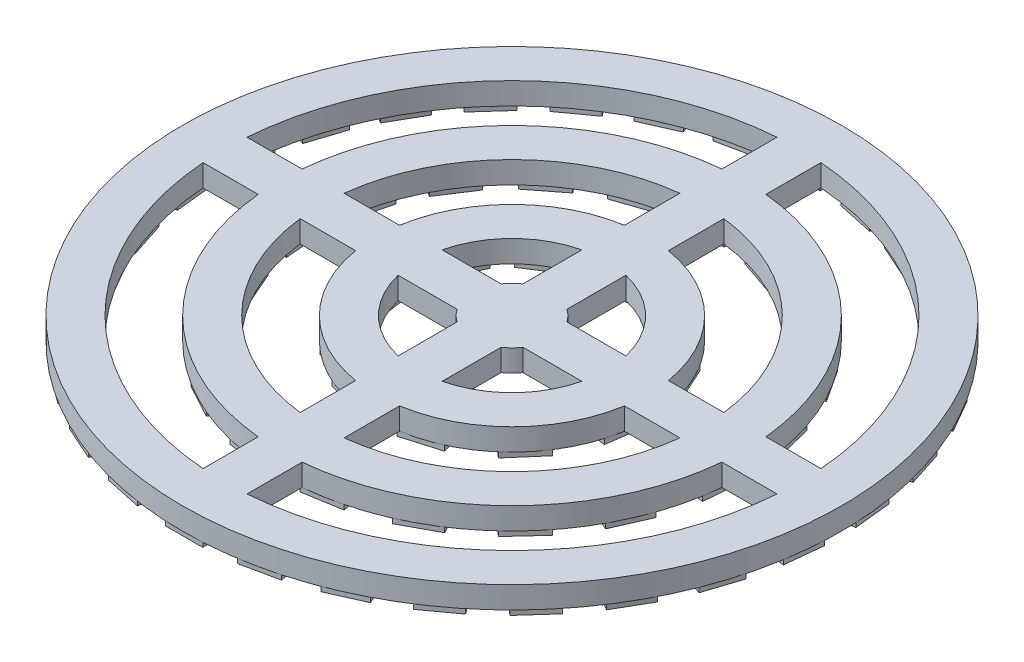
SolidWorks part; units mm, degrees
ref_plane "Front Plane" through (0, 0, 0) normal (0, 0, 1) x (1, 0, 0)
ref_plane "Top Plane" through (0, 0, 0) normal (0, 1, 0) x (1, 0, 0)
ref_plane "Right Plane" through (0, 0, 0) normal (1, 0, 0) x (0, 0, -1)
sketch "Sketch1" plane through (0, 0, 0) normal (0, 1, 0) x (1, 0, 0)
  circle A0 centre (0, 0) radius 30
  dimension "D1" = 60
extrude "Boss-Extrude1" add sketch "Sketch1" along normal blind 2
sketch "Sketch2" plane through (0, 2, 0) normal (0, 1, 0) x (1, 0, 0)
  line L0 (-30, 0) -> (30, 0) construction
  line L1 (-30, -2) -> (30, -2)
  line L2 (0, 30) -> (0, -30) construction
  line L3 (-2, 30) -> (-2, -30)
  line L4 (-30, 2) -> (30, 2)
  line L5 (2, 30) -> (2, -30)
  circle A0 centre (0, 0) radius 26.2
  circle A1 centre (0, 0) radius 21.2
  circle A2 centre (0, 0) radius 17.4
  circle A3 centre (0, 0) radius 12.4
  circle A4 centre (0, 0) radius 8.6
  circle A5 centre (0, 0) radius 30 construction
  circle A6 centre (0, 0) radius 3.6
  dimension "D3" = 3.8
  dimension "D4" = 3.8
  dimension "D5" = 3.8
  dimension "D6" = 5
  dimension "D7" = 5
  dimension "D8" = 5
  dimension "D1" = 2
  dimension "D2" = 2
extrude "Cut-Extrude1" cut sketch "Sketch2" against normal blind 2 contours A1 L1 A0 L3 | A1 L3 A0 L4 | A1 L4 A0 L5 | A1 L5 A0 L1 | A3 L5 A2 L1 | A3 L4 A2 L5 | A3 L3 A2 L4 | A3 L1 A2 L3 | A6 L1 A4 L3 | A6 L3 A4 L4 | A6 L4 A4 L5 | A6 L5 A4 L1
sketch "Sketch3" plane through (0, 0, 0) normal (0, -1, 0) x (-1, 0, 0)
  line L0 (0, 30) -> (0, 0) construction
  line L1 (-1.7, 26.35) -> (1.7, 26.35)
  line L2 (-1.7, 26.35) -> (-1.7, 29.85)
  line L3 (-1.7, 29.85) -> (1.7, 29.85)
  line L4 (1.7, 26.35) -> (1.7, 29.85)
  line L5 (-1.7, 26.35) -> (1.7, 29.85) construction
  line L6 (-1.7, 29.85) -> (1.7, 26.35) construction
  line L7 (7.1413, 25.4207) -> (7.869, 28.8443)
  line L8 (4.5433, 29.5512) -> (7.869, 28.8443)
  line L9 (3.8156, 26.1276) -> (4.5433, 29.5512)
  line L10 (3.8156, 26.1276) -> (7.1413, 25.4207)
  line L11 (12.2705, 23.3805) -> (13.6941, 26.5779)
  line L12 (10.5881, 27.9608) -> (13.6941, 26.5779)
  line L13 (9.1645, 24.7634) -> (10.5881, 27.9608)
  line L14 (9.1645, 24.7634) -> (12.2705, 23.3805)
  line L15 (16.8635, 20.3184) -> (18.9207, 23.1499)
  line L16 (16.1701, 25.1484) -> (18.9207, 23.1499)
  line L17 (14.1128, 22.3168) -> (16.1701, 25.1484)
  line L18 (14.1128, 22.3168) -> (16.8635, 20.3184)
  line L19 (20.7194, 16.3682) -> (23.3204, 18.7102)
  line L20 (21.0454, 21.2369) -> (23.3204, 18.7102)
  line L21 (18.4443, 18.8949) -> (21.0454, 21.2369)
  line L22 (18.4443, 18.8949) -> (20.7194, 16.3682)
  line L23 (23.6698, 11.7028) -> (26.7009, 13.4528)
  line L24 (25.0009, 16.3972) -> (26.7009, 13.4528)
  line L25 (21.9698, 14.6472) -> (25.0009, 16.3972)
  line L26 (21.9698, 14.6472) -> (23.6698, 11.7028)
  line L27 (25.5857, 6.5258) -> (28.9144, 7.6074)
  line L28 (27.8637, 10.841) -> (28.9144, 7.6074)
  line L29 (24.535, 9.7594) -> (27.8637, 10.841)
  line L30 (24.535, 9.7594) -> (25.5857, 6.5258)
  line L31 (26.3834, 1.0636) -> (29.8642, 1.4295)
  line L32 (29.5088, 4.8109) -> (29.8642, 1.4295)
  line L33 (26.028, 4.445) -> (29.5088, 4.8109)
  line L34 (26.028, 4.445) -> (26.3834, 1.0636)
  line L35 (26.028, -4.445) -> (29.5088, -4.8109)
  line L36 (29.8642, -1.4295) -> (29.5088, -4.8109)
  line L37 (26.3834, -1.0636) -> (29.8642, -1.4295)
  line L38 (26.3834, -1.0636) -> (26.028, -4.445)
  line L39 (24.535, -9.7594) -> (27.8637, -10.841)
  line L40 (28.9144, -7.6074) -> (27.8637, -10.841)
  line L41 (25.5857, -6.5258) -> (28.9144, -7.6074)
  line L42 (25.5857, -6.5258) -> (24.535, -9.7594)
  line L43 (21.9698, -14.6472) -> (25.0009, -16.3972)
  line L44 (26.7009, -13.4528) -> (25.0009, -16.3972)
  line L45 (23.6698, -11.7028) -> (26.7009, -13.4528)
  line L46 (23.6698, -11.7028) -> (21.9698, -14.6472)
  line L47 (18.4443, -18.8949) -> (21.0454, -21.2369)
  line L48 (23.3204, -18.7102) -> (21.0454, -21.2369)
  line L49 (20.7194, -16.3682) -> (23.3204, -18.7102)
  line L50 (20.7194, -16.3682) -> (18.4443, -18.8949)
  line L51 (14.1128, -22.3168) -> (16.1701, -25.1484)
  line L52 (18.9207, -23.1499) -> (16.1701, -25.1484)
  line L53 (16.8635, -20.3184) -> (18.9207, -23.1499)
  line L54 (16.8635, -20.3184) -> (14.1128, -22.3168)
  line L55 (9.1645, -24.7634) -> (10.5881, -27.9608)
  line L56 (13.6941, -26.5779) -> (10.5881, -27.9608)
  line L57 (12.2705, -23.3805) -> (13.6941, -26.5779)
  line L58 (12.2705, -23.3805) -> (9.1645, -24.7634)
  line L59 (3.8156, -26.1276) -> (4.5433, -29.5512)
  line L60 (7.869, -28.8443) -> (4.5433, -29.5512)
  line L61 (7.1413, -25.4207) -> (7.869, -28.8443)
  line L62 (7.1413, -25.4207) -> (3.8156, -26.1276)
  line L63 (-1.7, -26.35) -> (-1.7, -29.85)
  line L64 (1.7, -29.85) -> (-1.7, -29.85)
  line L65 (1.7, -26.35) -> (1.7, -29.85)
  line L66 (1.7, -26.35) -> (-1.7, -26.35)
  line L67 (-7.1413, -25.4207) -> (-7.869, -28.8443)
  line L68 (-4.5433, -29.5512) -> (-7.869, -28.8443)
  line L69 (-3.8156, -26.1276) -> (-4.5433, -29.5512)
  line L70 (-3.8156, -26.1276) -> (-7.1413, -25.4207)
  line L71 (-12.2705, -23.3805) -> (-13.6941, -26.5779)
  line L72 (-10.5881, -27.9608) -> (-13.6941, -26.5779)
  line L73 (-9.1645, -24.7634) -> (-10.5881, -27.9608)
  line L74 (-9.1645, -24.7634) -> (-12.2705, -23.3805)
  line L91 (5.1797, 20.4777) -> (8.4901, 19.3412)
  line L92 (-1.75, 21.05) -> (1.75, 21.05)
  line L93 (-1.75, 21.05) -> (-1.75, 17.55)
  line L94 (-1.75, 17.55) -> (1.75, 17.55)
  line L95 (1.75, 21.05) -> (1.75, 17.55)
  line L96 (-1.75, 21.05) -> (1.75, 17.55) construction
  line L97 (-1.75, 17.55) -> (1.75, 21.05) construction
  line L98 (8.4901, 19.3412) -> (7.3537, 16.0309)
  line L99 (4.0433, 17.1673) -> (7.3537, 16.0309)
  line L100 (5.1797, 20.4777) -> (4.0433, 17.1673)
  line L101 (11.5482, 17.6863) -> (14.3102, 15.5365)
  line L102 (14.3102, 15.5365) -> (12.1604, 12.7745)
  line L103 (9.3984, 14.9243) -> (12.1604, 12.7745)
  line L104 (11.5482, 17.6863) -> (9.3984, 14.9243)
  line L105 (16.6652, 12.9783) -> (18.5795, 10.0482)
  line L106 (18.5795, 10.0482) -> (15.6494, 8.1339)
  line L107 (13.7351, 11.064) -> (15.6494, 8.1339)
  line L108 (16.6652, 12.9783) -> (13.7351, 11.064)
  line L109 (19.9763, 6.8639) -> (20.8355, 3.471)
  line L110 (20.8355, 3.471) -> (17.4426, 2.6118)
  line L111 (16.5834, 6.0047) -> (17.4426, 2.6118)
  line L112 (19.9763, 6.8639) -> (16.5834, 6.0047)
  line L113 (21.1226, 0.0057) -> (20.8336, -3.4823)
  line L114 (20.8336, -3.4823) -> (17.3455, -3.1933)
  line L115 (17.6346, 0.2948) -> (17.3455, -3.1933)
  line L116 (21.1226, 0.0057) -> (17.6346, 0.2948)
  line L117 (19.98, -6.8531) -> (18.5741, -10.0583)
  line L118 (18.5741, -10.0583) -> (15.3689, -8.6524)
  line L119 (16.7748, -5.4472) -> (15.3689, -8.6524)
  line L120 (19.98, -6.8531) -> (16.7748, -5.4472)
  line L121 (16.6722, -12.9693) -> (14.3017, -15.5443)
  line L122 (14.3017, -15.5443) -> (11.7267, -13.1738)
  line L123 (14.0972, -10.5988) -> (11.7267, -13.1738)
  line L124 (16.6722, -12.9693) -> (14.0972, -10.5988)
  line L125 (11.5578, -17.68) -> (8.4796, -19.3458)
  line L126 (8.4796, -19.3458) -> (6.8138, -16.2677)
  line L127 (9.892, -14.6019) -> (6.8138, -16.2677)
  line L128 (11.5578, -17.68) -> (9.892, -14.6019)
  line L129 (5.1908, -20.4749) -> (1.7386, -21.0509)
  line L130 (1.7386, -21.0509) -> (1.1625, -17.5987)
  line L131 (4.6148, -17.0226) -> (1.1625, -17.5987)
  line L132 (5.1908, -20.4749) -> (4.6148, -17.0226)
  line L133 (-1.7386, -21.0509) -> (-5.1908, -20.4749)
  line L134 (-5.1908, -20.4749) -> (-4.6148, -17.0226)
  line L135 (-1.1625, -17.5987) -> (-4.6148, -17.0226)
  line L136 (-1.7386, -21.0509) -> (-1.1625, -17.5987)
  line L137 (-8.4796, -19.3458) -> (-11.5578, -17.68)
  line L138 (-11.5578, -17.68) -> (-9.892, -14.6019)
  line L139 (-6.8138, -16.2677) -> (-9.892, -14.6019)
  line L140 (-8.4796, -19.3458) -> (-6.8138, -16.2677)
  line L149 (5.1507, 11.2515) -> (8.095, 9.3592)
  line L150 (-1.75, 8.75) -> (1.75, 8.75)
  line L151 (-1.75, 8.75) -> (-1.75, 12.25)
  line L152 (-1.75, 12.25) -> (1.75, 12.25)
  line L153 (1.75, 8.75) -> (1.75, 12.25)
  line L154 (-1.75, 8.75) -> (1.75, 12.25) construction
  line L155 (-1.75, 12.25) -> (1.75, 8.75) construction
  line L156 (6.2028, 6.4148) -> (8.095, 9.3592)
  line L157 (3.2584, 8.3071) -> (6.2028, 6.4148)
  line L158 (3.2584, 8.3071) -> (5.1507, 11.2515)
  line L159 (10.416, 6.6807) -> (11.87, 3.497)
  line L160 (8.6863, 2.043) -> (11.87, 3.497)
  line L161 (7.2323, 5.2267) -> (8.6863, 2.043)
  line L162 (7.2323, 5.2267) -> (10.416, 6.6807)
  line L163 (12.3744, -0.0112) -> (11.8763, -3.4755)
  line L164 (8.4119, -2.9774) -> (11.8763, -3.4755)
  line L165 (8.91, 0.4869) -> (8.4119, -2.9774)
  line L166 (8.91, 0.4869) -> (12.3744, -0.0112)
  line L167 (10.4039, -6.6995) -> (8.1119, -9.3446)
  line L168 (5.4668, -7.0526) -> (8.1119, -9.3446)
  line L169 (7.7588, -4.4075) -> (5.4668, -7.0526)
  line L170 (7.7588, -4.4075) -> (10.4039, -6.6995)
  line L171 (5.1303, -11.2608) -> (1.7721, -12.2468)
  line L172 (0.786, -8.8886) -> (1.7721, -12.2468)
  line L173 (4.1443, -7.9025) -> (0.786, -8.8886)
  line L174 (4.1443, -7.9025) -> (5.1303, -11.2608)
  line L175 (-1.7721, -12.2468) -> (-5.1303, -11.2608)
  line L176 (-4.1443, -7.9025) -> (-5.1303, -11.2608)
  line L177 (-0.786, -8.8886) -> (-4.1443, -7.9025)
  line L178 (-0.786, -8.8886) -> (-1.7721, -12.2468)
  line L179 (-8.1119, -9.3446) -> (-10.4039, -6.6995)
  line L180 (-7.7588, -4.4075) -> (-10.4039, -6.6995)
  line L181 (-5.4668, -7.0526) -> (-7.7588, -4.4075)
  line L182 (-5.4668, -7.0526) -> (-8.1119, -9.3446)
  line L184 (1.75, -1.75) -> (-1.75, -1.75)
  line L185 (1.75, -1.75) -> (1.75, 1.75)
  line L186 (1.75, 1.75) -> (-1.75, 1.75)
  line L187 (-1.75, -1.75) -> (-1.75, 1.75)
  line L188 (1.75, -1.75) -> (-1.75, 1.75) construction
  line L189 (1.75, 1.75) -> (-1.75, -1.75) construction
  line L190 (-16.8635, -20.3184) -> (-18.9207, -23.1499)
  line L191 (-16.1701, -25.1484) -> (-18.9207, -23.1499)
  line L192 (-14.1128, -22.3168) -> (-16.1701, -25.1484)
  line L193 (-14.1128, -22.3168) -> (-16.8635, -20.3184)
  line L194 (-20.7194, -16.3682) -> (-23.3204, -18.7102)
  line L195 (-21.0454, -21.2369) -> (-23.3204, -18.7102)
  line L196 (-18.4443, -18.8949) -> (-21.0454, -21.2369)
  line L197 (-18.4443, -18.8949) -> (-20.7194, -16.3682)
  line L198 (-11.8763, -3.4755) -> (-12.3744, -0.0112)
  line L199 (-8.91, 0.4869) -> (-12.3744, -0.0112)
  line L200 (-8.4119, -2.9774) -> (-8.91, 0.4869)
  line L201 (-8.4119, -2.9774) -> (-11.8763, -3.4755)
  line L202 (-11.87, 3.497) -> (-10.416, 6.6807)
  line L203 (-7.2323, 5.2267) -> (-10.416, 6.6807)
  line L204 (-8.6863, 2.043) -> (-7.2323, 5.2267)
  line L205 (-8.6863, 2.043) -> (-11.87, 3.497)
  line L206 (-8.095, 9.3592) -> (-5.1507, 11.2515)
  line L207 (-3.2584, 8.3071) -> (-5.1507, 11.2515)
  line L208 (-6.2028, 6.4148) -> (-3.2584, 8.3071)
  line L209 (-6.2028, 6.4148) -> (-8.095, 9.3592)
  line L210 (-14.3017, -15.5443) -> (-16.6722, -12.9693)
  line L211 (-16.6722, -12.9693) -> (-14.0972, -10.5988)
  line L212 (-11.7267, -13.1738) -> (-14.0972, -10.5988)
  line L213 (-14.3017, -15.5443) -> (-11.7267, -13.1738)
  line L214 (-18.5741, -10.0583) -> (-19.98, -6.8531)
  line L215 (-19.98, -6.8531) -> (-16.7748, -5.4472)
  line L216 (-15.3689, -8.6524) -> (-16.7748, -5.4472)
  line L217 (-18.5741, -10.0583) -> (-15.3689, -8.6524)
  line L218 (-20.8336, -3.4823) -> (-21.1226, 0.0057)
  line L219 (-21.1226, 0.0057) -> (-17.6346, 0.2948)
  line L220 (-17.3455, -3.1933) -> (-17.6346, 0.2948)
  line L221 (-20.8336, -3.4823) -> (-17.3455, -3.1933)
  line L222 (-20.8355, 3.471) -> (-19.9763, 6.8639)
  line L223 (-19.9763, 6.8639) -> (-16.5834, 6.0047)
  line L224 (-17.4426, 2.6118) -> (-16.5834, 6.0047)
  line L225 (-20.8355, 3.471) -> (-17.4426, 2.6118)
  line L226 (-18.5795, 10.0482) -> (-16.6652, 12.9783)
  line L227 (-16.6652, 12.9783) -> (-13.7351, 11.064)
  line L228 (-15.6494, 8.1339) -> (-13.7351, 11.064)
  line L229 (-18.5795, 10.0482) -> (-15.6494, 8.1339)
  line L230 (-14.3102, 15.5365) -> (-11.5482, 17.6863)
  line L231 (-11.5482, 17.6863) -> (-9.3984, 14.9243)
  line L232 (-12.1604, 12.7745) -> (-9.3984, 14.9243)
  line L233 (-14.3102, 15.5365) -> (-12.1604, 12.7745)
  line L234 (-8.4901, 19.3412) -> (-5.1797, 20.4777)
  line L235 (-5.1797, 20.4777) -> (-4.0433, 17.1673)
  line L236 (-7.3537, 16.0309) -> (-4.0433, 17.1673)
  line L237 (-8.4901, 19.3412) -> (-7.3537, 16.0309)
  line L238 (-23.6698, -11.7028) -> (-26.7009, -13.4528)
  line L239 (-25.0009, -16.3972) -> (-26.7009, -13.4528)
  line L240 (-21.9698, -14.6472) -> (-25.0009, -16.3972)
  line L241 (-21.9698, -14.6472) -> (-23.6698, -11.7028)
  line L242 (-25.5857, -6.5258) -> (-28.9144, -7.6074)
  line L243 (-27.8637, -10.841) -> (-28.9144, -7.6074)
  line L244 (-24.535, -9.7594) -> (-27.8637, -10.841)
  line L245 (-24.535, -9.7594) -> (-25.5857, -6.5258)
  line L246 (-26.3834, -1.0636) -> (-29.8642, -1.4295)
  line L247 (-29.5088, -4.8109) -> (-29.8642, -1.4295)
  line L248 (-26.028, -4.445) -> (-29.5088, -4.8109)
  line L249 (-26.028, -4.445) -> (-26.3834, -1.0636)
  line L250 (-26.028, 4.445) -> (-29.5088, 4.8109)
  line L251 (-29.8642, 1.4295) -> (-29.5088, 4.8109)
  line L252 (-26.3834, 1.0636) -> (-29.8642, 1.4295)
  line L253 (-26.3834, 1.0636) -> (-26.028, 4.445)
  line L254 (-24.535, 9.7594) -> (-27.8637, 10.841)
  line L255 (-28.9144, 7.6074) -> (-27.8637, 10.841)
  line L256 (-25.5857, 6.5258) -> (-28.9144, 7.6074)
  line L257 (-25.5857, 6.5258) -> (-24.535, 9.7594)
  line L258 (-21.9698, 14.6472) -> (-25.0009, 16.3972)
  line L259 (-26.7009, 13.4528) -> (-25.0009, 16.3972)
  line L260 (-23.6698, 11.7028) -> (-26.7009, 13.4528)
  line L261 (-23.6698, 11.7028) -> (-21.9698, 14.6472)
  line L262 (-18.4443, 18.8949) -> (-21.0454, 21.2369)
  line L263 (-23.3204, 18.7102) -> (-21.0454, 21.2369)
  line L264 (-20.7194, 16.3682) -> (-23.3204, 18.7102)
  line L265 (-20.7194, 16.3682) -> (-18.4443, 18.8949)
  line L266 (-14.1128, 22.3168) -> (-16.1701, 25.1484)
  line L267 (-18.9207, 23.1499) -> (-16.1701, 25.1484)
  line L268 (-16.8635, 20.3184) -> (-18.9207, 23.1499)
  line L269 (-16.8635, 20.3184) -> (-14.1128, 22.3168)
  line L270 (-9.1645, 24.7634) -> (-10.5881, 27.9608)
  line L271 (-13.6941, 26.5779) -> (-10.5881, 27.9608)
  line L272 (-12.2705, 23.3805) -> (-13.6941, 26.5779)
  line L273 (-12.2705, 23.3805) -> (-9.1645, 24.7634)
  line L274 (-3.8156, 26.1276) -> (-4.5433, 29.5512)
  line L275 (-7.869, 28.8443) -> (-4.5433, 29.5512)
  line L276 (-7.1413, 25.4207) -> (-7.869, 28.8443)
  line L277 (-7.1413, 25.4207) -> (-3.8156, 26.1276)
  line L278 (0, 0) -> (-22.2943, -20.0739) construction
  circle A0 centre (0, 0) radius 30 construction
  circle A1 centre (0, 0) radius 30 construction
  point P0 (0, 28.1)
  point P10 (0, 19.3)
  point P99 (0, 10.5)
  dimension "D1" = 3.5
  dimension "D2" = 3.4
  dimension "D3" = 1.9
  dimension "D5" = 3.5
  dimension "D6" = 3.5
  dimension "D7" = 10.7
  dimension "D9" = 3.5
  dimension "D10" = 3.5
  dimension "D11" = 19.5
  dimension "D13" = 3.5
  dimension "D4" = 30
  dimension "D8" = 19
  dimension "D12" = 11
extrude "Boss-Extrude2" add sketch "Sketch3" along normal blind 0.5
equation "\"D4@Sketch2\"=\"D3@Sketch2\""
equation "\"D5@Sketch2\"=\"D3@Sketch2\""
equation "\"D6@Sketch2\"=\"D7@Sketch2\""
equation "\"D8@Sketch2\"=\"D7@Sketch2\""
equation "\"D11@Sketch3\"=5+5+7+0.6+3.8/2mm"
